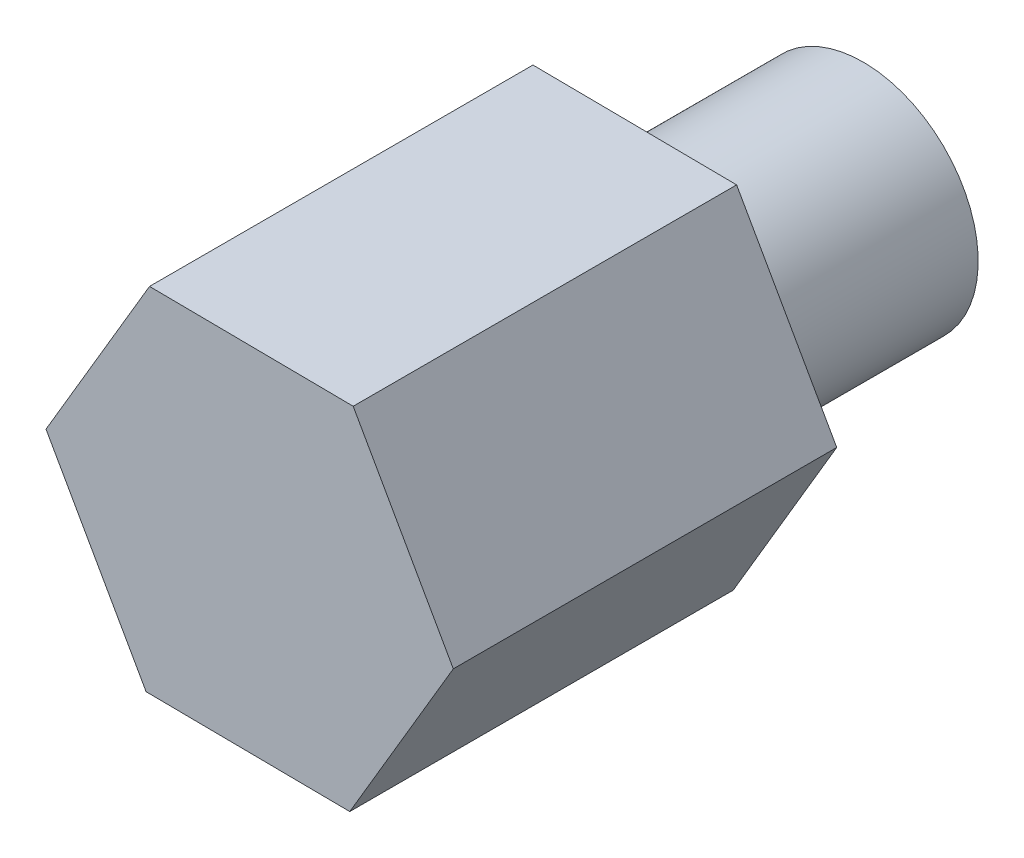
SolidWorks part; units mm, degrees
ref_plane "前视基准面" through (0, 0, 0) normal (0, 0, 1) x (1, 0, 0)
ref_plane "上视基准面" through (0, 0, 0) normal (0, 1, 0) x (1, 0, 0)
ref_plane "右视基准面" through (0, 0, 0) normal (1, 0, 0) x (0, 0, -1)
sketch "草图1" plane through (0, 0, 0) normal (0, 0, 1) x (1, 0, 0)
  line L1 (1.3056, -2.3128) -> (2.6557, -0.0257)
  line L2 (2.6557, -0.0257) -> (1.3501, 2.287)
  line L3 (1.3501, 2.287) -> (-1.3056, 2.3128)
  line L4 (-1.3056, 2.3128) -> (-2.6557, 0.0257)
  line L5 (-2.6557, 0.0257) -> (-1.3501, -2.287)
  line L6 (-1.3501, -2.287) -> (1.3056, -2.3128)
  circle A0 centre (0, 0) radius 2.3 construction
  dimension "D1" = 4.6
extrude "凸台-拉伸1" add sketch "草图1" along normal blind 5
sketch "草图2" plane through (0, 0, 0) normal (0, 0, -1) x (-1, 0, 0)
  circle A0 centre (0, 0) radius 1.5
  dimension "D1" = 3
extrude "凸台-拉伸2" add sketch "草图2" along normal blind 3
